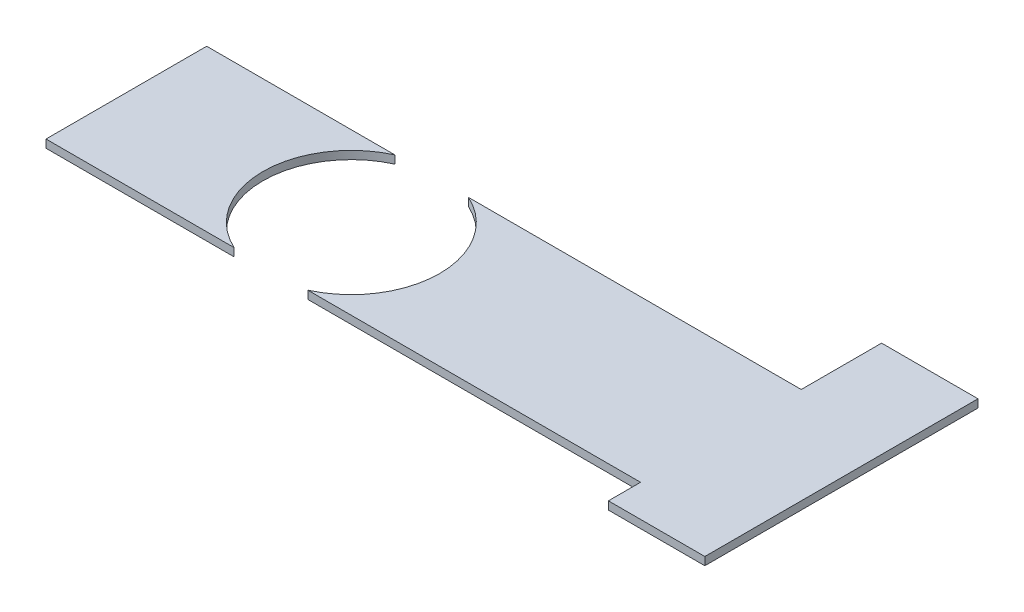
SolidWorks part; units mm, degrees
ref_plane "Front" through (0, 0, 0) normal (0, 0, 1) x (1, 0, 0)
ref_plane "Top" through (0, 0, 0) normal (0, 1, 0) x (1, 0, 0)
ref_plane "Right" through (0, 0, 0) normal (1, 0, 0) x (0, 0, -1)
sketch "草图1" plane through (0, 0, 0) normal (0, 1, 0) x (1, 0, 0)
  line L0 (-11.322, 5) -> (25.678, 5)
  line L1 (25.678, 5) -> (25.678, 10)
  line L2 (25.678, 10) -> (31.678, 10)
  line L3 (31.678, 10) -> (31.678, -7)
  line L4 (31.678, -7) -> (25.678, -7)
  line L5 (25.678, -7) -> (25.678, -5)
  line L6 (25.678, -5) -> (-11.322, -5)
  line L7 (-11.322, -5) -> (-11.322, 5)
  line L8 (0, 0) -> (-35.322, 0) construction
  dimension "D1" = 6
  dimension "D2" = 2
  dimension "D3" = 5
  dimension "D4" = 5
  dimension "D5" = 37
  dimension "D6" = 37
  dimension "D7" = 6
extrude "凸台-拉伸1" add sketch "草图1" along normal blind 0.5
sketch "草图2" plane through (0, 0, 0) normal (0, -1, 0) x (1, 0, 0)
  line L0 (-26.2694, 0) -> (42.0879, 0) construction
  line L1 (31.678, 7) -> (31.678, -10) construction
  circle A0 centre (2.678, 0) radius 5.5
  dimension "D1" = 11
  dimension "D2" = 29
extrude "切除-拉伸1" cut sketch "草图2" against normal through all
